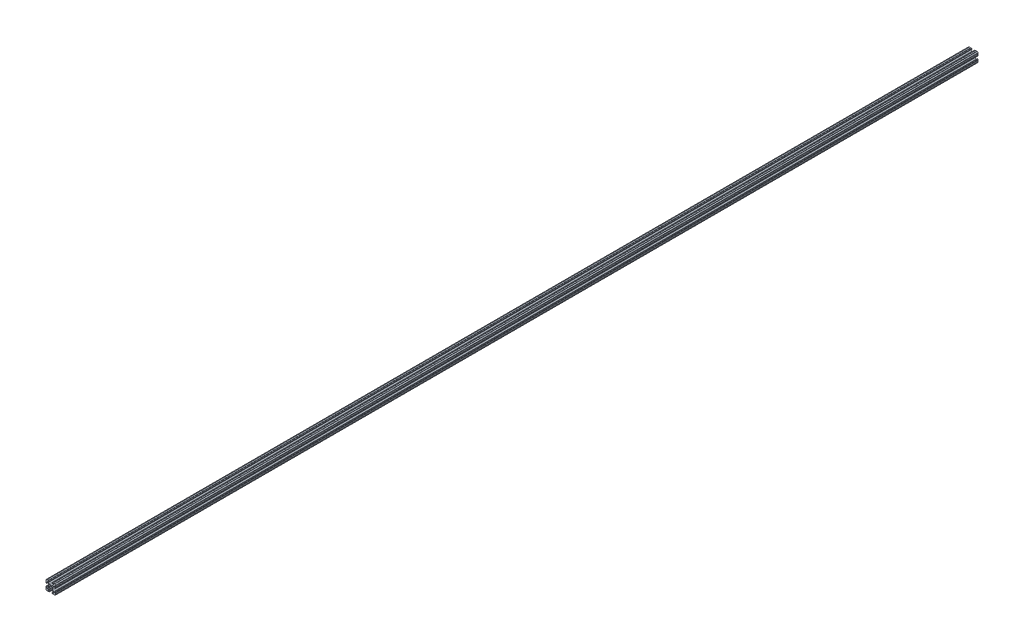
SolidWorks part; units mm, degrees
ref_plane "Front Plane" through (0, 0, 0) normal (0, 0, 1) x (1, 0, 0)
ref_plane "Top Plane" through (0, 0, 0) normal (0, 1, 0) x (1, 0, 0)
ref_plane "Right Plane" through (0, 0, 0) normal (1, 0, 0) x (0, 0, -1)
sketch "Sketch1" plane through (0, 0, 0) normal (0, 0, 1) x (1, 0, 0)
  line L88 (-7.1797, -8.6452) -> (-3.9523, -5.4237)
  line L89 (-1.7093, -4.4958) -> (1.7093, -4.4958)
  line L90 (3.9523, -5.4237) -> (7.1797, -8.6452)
  line L91 (6.4164, -10.4902) -> (4.2875, -10.4902)
  line L92 (3.2385, -11.5392) -> (3.2385, -11.651)
  line L93 (4.2875, -12.7) -> (5.3171, -12.7)
  line L94 (6.3331, -12.7) -> (9.5504, -12.7)
  line L95 (12.7, -9.5504) -> (12.7, -6.3331)
  line L96 (12.7, -5.3171) -> (12.7, -4.2875)
  line L97 (11.651, -3.2385) -> (11.5392, -3.2385)
  line L98 (10.4902, -4.2875) -> (10.4902, -6.4021)
  line L99 (8.7371, -7.1294) -> (5.441, -3.8408)
  line L100 (4.5085, -1.5932) -> (4.5085, 1.5932)
  line L101 (5.441, 3.8408) -> (8.7371, 7.1294)
  line L102 (10.4902, 6.4021) -> (10.4902, 4.2875)
  line L103 (11.5392, 3.2385) -> (11.651, 3.2385)
  line L104 (12.7, 4.2875) -> (12.7, 5.3171)
  line L105 (12.7, 6.3331) -> (12.7, 9.5504)
  line L106 (9.5504, 12.7) -> (6.3331, 12.7)
  line L107 (5.3171, 12.7) -> (4.2875, 12.7)
  line L108 (3.2385, 11.651) -> (3.2385, 11.5392)
  line L109 (4.2875, 10.4902) -> (6.4768, 10.4902)
  line L110 (7.207, 8.7244) -> (3.8983, 5.4232)
  line L111 (1.6558, 4.4958) -> (-1.6558, 4.4958)
  line L112 (-3.8983, 5.4232) -> (-7.207, 8.7244)
  line L113 (-6.4768, 10.4902) -> (-4.2875, 10.4902)
  line L114 (-3.2385, 11.5392) -> (-3.2385, 11.651)
  line L115 (-4.2875, 12.7) -> (-5.3171, 12.7)
  line L116 (-6.3331, 12.7) -> (-9.5504, 12.7)
  line L117 (-12.7, 9.5504) -> (-12.7, 6.3331)
  line L118 (-12.7, 5.3171) -> (-12.7, 4.2875)
  line L119 (-11.651, 3.2385) -> (-11.5392, 3.2385)
  line L120 (-10.4902, 4.2875) -> (-10.4902, 6.4021)
  line L121 (-8.7371, 7.1294) -> (-5.441, 3.8408)
  line L122 (-4.5085, 1.5932) -> (-4.5085, -1.5932)
  line L123 (-5.441, -3.8408) -> (-8.7371, -7.1294)
  line L124 (-10.4902, -6.4021) -> (-10.4902, -4.2875)
  line L125 (-11.5392, -3.2385) -> (-11.651, -3.2385)
  line L126 (-12.7, -4.2875) -> (-12.7, -5.3171)
  line L127 (-12.7, -6.3331) -> (-12.7, -9.5504)
  line L128 (-9.5504, -12.7) -> (-6.3331, -12.7)
  line L129 (-5.3171, -12.7) -> (-4.2875, -12.7)
  line L130 (-3.2385, -11.651) -> (-3.2385, -11.5392)
  line L131 (-4.2875, -10.4902) -> (-6.4164, -10.4902)
  circle A1 centre (0, 0) radius 2.6035
  arc A104 (-7.1797, -8.6452) -> (-6.4164, -10.4902) centre (-6.4164, -9.4098) ccw
  arc A105 (-1.7093, -4.4958) -> (-3.9523, -5.4237) centre (-1.7093, -7.6708) ccw
  arc A106 (3.9523, -5.4237) -> (1.7093, -4.4958) centre (1.7093, -7.6708) ccw
  arc A107 (6.4164, -10.4902) -> (7.1797, -8.6452) centre (6.4164, -9.4098) ccw
  arc A108 (4.2875, -10.4902) -> (3.2385, -11.5392) centre (4.2875, -11.5392) ccw
  arc A109 (3.2385, -11.651) -> (4.2875, -12.7) centre (4.2875, -11.651) ccw
  arc A110 (6.3331, -12.7) -> (5.3171, -12.7) centre (5.8251, -12.7) ccw
  arc A111 (10.5664, -12.6998) -> (9.5504, -12.7) centre (10.0584, -12.7) ccw
  arc A112 (10.5664, -12.6998) -> (12.6998, -10.5664) centre (10.5918, -10.5918) ccw
  arc A113 (12.7, -9.5504) -> (12.6998, -10.5664) centre (12.7, -10.0584) ccw
  arc A114 (12.7, -5.3171) -> (12.7, -6.3331) centre (12.7, -5.8251) ccw
  arc A115 (12.7, -4.2875) -> (11.651, -3.2385) centre (11.651, -4.2875) ccw
  arc A116 (11.5392, -3.2385) -> (10.4902, -4.2875) centre (11.5392, -4.2875) ccw
  arc A117 (8.7371, -7.1294) -> (10.4902, -6.4021) centre (9.4628, -6.4021) ccw
  arc A118 (4.5085, -1.5932) -> (5.441, -3.8408) centre (7.6835, -1.5932) ccw
  arc A119 (5.441, 3.8408) -> (4.5085, 1.5932) centre (7.6835, 1.5932) ccw
  arc A120 (10.4902, 6.4021) -> (8.7371, 7.1294) centre (9.4628, 6.4021) ccw
  arc A121 (10.4902, 4.2875) -> (11.5392, 3.2385) centre (11.5392, 4.2875) ccw
  arc A122 (11.651, 3.2385) -> (12.7, 4.2875) centre (11.651, 4.2875) ccw
  arc A123 (12.7, 6.3331) -> (12.7, 5.3171) centre (12.7, 5.8251) ccw
  arc A124 (12.6998, 10.5664) -> (12.7, 9.5504) centre (12.7, 10.0584) ccw
  arc A125 (12.6998, 10.5664) -> (10.5664, 12.6998) centre (10.5918, 10.5918) ccw
  arc A126 (9.5504, 12.7) -> (10.5664, 12.6998) centre (10.0584, 12.7) ccw
  arc A127 (5.3171, 12.7) -> (6.3331, 12.7) centre (5.8251, 12.7) ccw
  arc A128 (4.2875, 12.7) -> (3.2385, 11.651) centre (4.2875, 11.651) ccw
  arc A129 (3.2385, 11.5392) -> (4.2875, 10.4902) centre (4.2875, 11.5392) ccw
  arc A130 (7.207, 8.7244) -> (6.4768, 10.4902) centre (6.4768, 9.4563) ccw
  arc A131 (1.6558, 4.4958) -> (3.8983, 5.4232) centre (1.6558, 7.6708) ccw
  arc A132 (-3.8983, 5.4232) -> (-1.6558, 4.4958) centre (-1.6558, 7.6708) ccw
  arc A133 (-6.4768, 10.4902) -> (-7.207, 8.7244) centre (-6.4768, 9.4563) ccw
  arc A134 (-4.2875, 10.4902) -> (-3.2385, 11.5392) centre (-4.2875, 11.5392) ccw
  arc A135 (-3.2385, 11.651) -> (-4.2875, 12.7) centre (-4.2875, 11.651) ccw
  arc A136 (-6.3331, 12.7) -> (-5.3171, 12.7) centre (-5.8251, 12.7) ccw
  arc A137 (-10.5664, 12.6998) -> (-9.5504, 12.7) centre (-10.0584, 12.7) ccw
  arc A138 (-10.5664, 12.6998) -> (-12.6998, 10.5664) centre (-10.5918, 10.5918) ccw
  arc A139 (-12.7, 9.5504) -> (-12.6998, 10.5664) centre (-12.7, 10.0584) ccw
  arc A140 (-12.7, 5.3171) -> (-12.7, 6.3331) centre (-12.7, 5.8251) ccw
  arc A141 (-12.7, 4.2875) -> (-11.651, 3.2385) centre (-11.651, 4.2875) ccw
  arc A142 (-11.5392, 3.2385) -> (-10.4902, 4.2875) centre (-11.5392, 4.2875) ccw
  arc A143 (-8.7371, 7.1294) -> (-10.4902, 6.4021) centre (-9.4628, 6.4021) ccw
  arc A144 (-4.5085, 1.5932) -> (-5.441, 3.8408) centre (-7.6835, 1.5932) ccw
  arc A145 (-5.441, -3.8408) -> (-4.5085, -1.5932) centre (-7.6835, -1.5932) ccw
  arc A146 (-10.4902, -6.4021) -> (-8.7371, -7.1294) centre (-9.4628, -6.4021) ccw
  arc A147 (-10.4902, -4.2875) -> (-11.5392, -3.2385) centre (-11.5392, -4.2875) ccw
  arc A148 (-11.651, -3.2385) -> (-12.7, -4.2875) centre (-11.651, -4.2875) ccw
  arc A149 (-12.7, -6.3331) -> (-12.7, -5.3171) centre (-12.7, -5.8251) ccw
  arc A150 (-12.6998, -10.5664) -> (-12.7, -9.5504) centre (-12.7, -10.0584) ccw
  arc A151 (-12.6998, -10.5664) -> (-10.5664, -12.6998) centre (-10.5918, -10.5918) ccw
  arc A152 (-9.5504, -12.7) -> (-10.5664, -12.6998) centre (-10.0584, -12.7) ccw
  arc A153 (-5.3171, -12.7) -> (-6.3331, -12.7) centre (-5.8251, -12.7) ccw
  arc A154 (-4.2875, -12.7) -> (-3.2385, -11.651) centre (-4.2875, -11.651) ccw
  arc A155 (-3.2385, -11.5392) -> (-4.2875, -10.4902) centre (-4.2875, -11.5392) ccw
extrude "Boss-Extrude1" add sketch "Sketch1" along normal mid plane 2438.4
